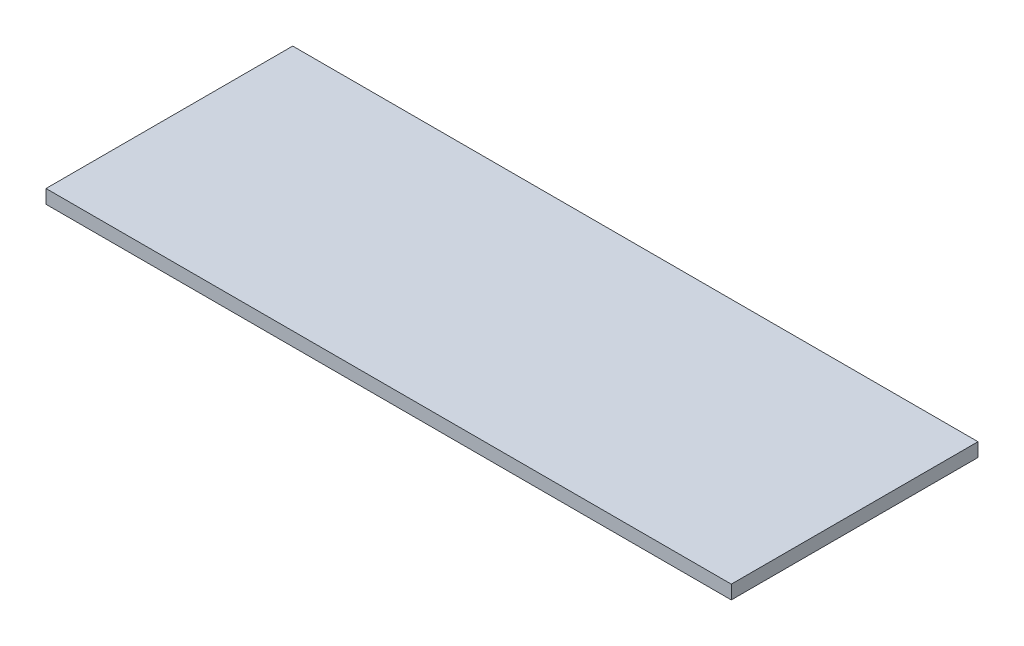
SolidWorks part; units mm, degrees
ref_plane "Front Plane" through (0, 0, 0) normal (0, 0, 1) x (1, 0, 0)
ref_plane "Top Plane" through (0, 0, 0) normal (0, 1, 0) x (1, 0, 0)
ref_plane "Right Plane" through (0, 0, 0) normal (1, 0, 0) x (0, 0, -1)
sketch "Sketch1" plane through (0, 0, 0) normal (0, 1, 0) x (1, 0, 0)
  line L1 (-125, 45) -> (125, 45)
  line L2 (-125, 45) -> (-125, -45)
  line L3 (-125, -45) -> (125, -45)
  line L4 (125, 45) -> (125, -45)
  line L5 (-125, 45) -> (125, -45) construction
  line L6 (-125, -45) -> (125, 45) construction
  point P0 (0, 0)
  dimension "D1" = 250
  dimension "D2" = 90
extrude "Boss-Extrude1" add sketch "Sketch1" along normal blind 5
